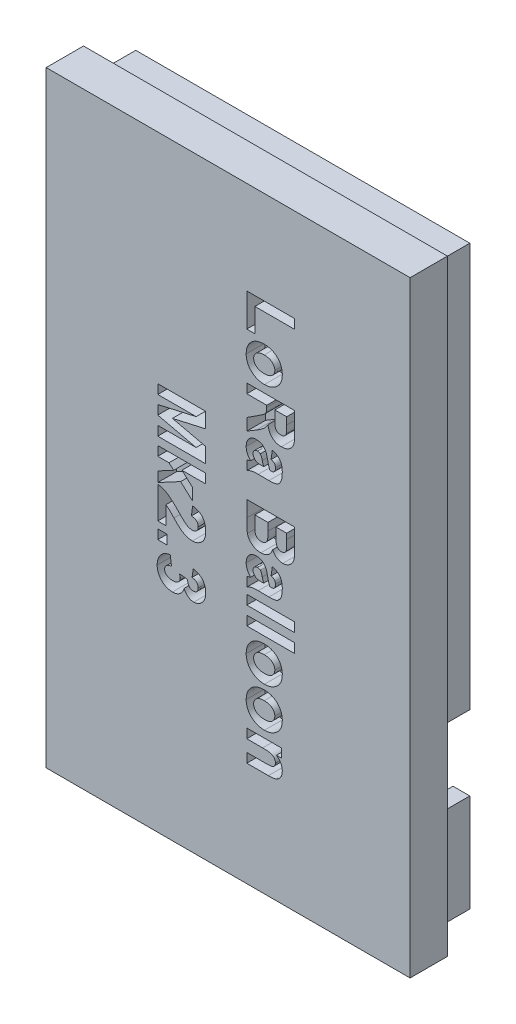
SolidWorks part; units mm, degrees
ref_plane "Front Plane" through (0, 0, 0) normal (0, 0, 1) x (1, 0, 0)
ref_plane "Top Plane" through (0, 0, 0) normal (0, 1, 0) x (1, 0, 0)
ref_plane "Right Plane" through (0, 0, 0) normal (1, 0, 0) x (0, 0, -1)
sketch "Sketch1" plane through (0, 0, 0) normal (0, 0, 1) x (1, 0, 0)
  line L1 (0, 0) -> (39, 0)
  line L2 (0, 0) -> (0, 65)
  line L3 (0, 65) -> (39, 65)
  line L4 (39, 0) -> (39, 65)
  dimension "D1" = 65
  dimension "D2" = 39
extrude "Base" add sketch "Sketch1" along normal blind 4
sketch "Sketch2" plane through (0, 0, 0) normal (0, 0, -1) x (-1, 0, 0)
  line L0 (-39, 0) -> (-39, 65) construction
  line L1 (-37.4, 63.4) -> (-35.6, 63.4)
  line L2 (-37.4, 63.4) -> (-37.4, 1.6)
  line L3 (-37.4, 1.6) -> (-35.6, 1.6)
  line L4 (-35.6, 63.4) -> (-35.6, 1.6)
  line L5 (0, 0) -> (-39, 0) construction
  line L6 (0, 65) -> (0, 0) construction
  line L7 (-35.6, 1.6) -> (-1.6, 1.6)
  line L8 (-35.6, 1.6) -> (-35.6, 3.4)
  line L9 (-35.6, 3.4) -> (-1.6, 3.4)
  line L10 (-1.6, 1.6) -> (-1.6, 3.4)
  line L12 (-39, 65) -> (0, 65) construction
  line L13 (-39, 32.5) -> (0, 32.5) construction
  line L14 (-19.5, 65) -> (-19.5, 0) construction
  line L15 (-35.6, 61.6) -> (-1.6, 61.6)
  line L16 (-1.6, 63.4) -> (-1.6, 61.6)
  line L17 (-35.6, 63.4) -> (-1.6, 63.4)
  line L18 (-35.6, 63.4) -> (-35.6, 61.6)
  line L19 (-1.6, 1.6) -> (-3.4, 1.6)
  line L20 (-3.4, 63.4) -> (-3.4, 1.6)
  line L21 (-1.6, 63.4) -> (-3.4, 63.4)
  line L22 (-1.6, 63.4) -> (-1.6, 1.6)
  dimension "D1" = 1.6
  dimension "D2" = 1.8
  dimension "D3" = 1.6
  dimension "D4" = 1.8
extrude "Mount" add sketch "Sketch2" along normal blind 4 contours L4 L1 L2 L3 | L22 L15 L20 L9 | L20 L9 L4 L7 | L9 L20 L7 L10 | L17 L20 L15 L16 | L20 L17 L4 L15
sketch "Sketch3" plane through (0, 0, 4) normal (0, 0, 1) x (1, 0, 0)
  line L0 (21.5, 0) -> (21.5, 65) construction
  line L1 (19.5, 0) -> (19.5, 5) construction
  line L2 (19.5, 65) -> (19.5, 60) construction
  line L3 (39, 65) -> (0, 65) construction
  line L4 (0, 0) -> (39, 0) construction
  line L5 (39, 32.5) -> (28, 32.5) construction
  line L6 (0, 65) -> (0, 0) construction
  line L7 (39, 0) -> (39, 65) construction
  line L8 (0, 32.5) -> (11, 32.5) construction
  text T0 "<b>  LoRa Balloon </b>\r\n<b>Mk2.3</b>" font "Arial Narrow" height in points 20
  dimension "D1" = 21.5
  dimension "D2" = 65
  dimension "D3" = 5
  dimension "D4" = 5
  dimension "D5" = 11
extrude "Name" cut sketch "Sketch3" against normal blind 2
sketch "Sketch4" plane through (35.6, 0, 0) normal (-1, 0, 0) x (0, 0, 1)
  line L0 (0, 61.6) -> (0, 3.4) construction
  line L1 (0, 20.1) -> (-4, 20.1)
  line L2 (0, 20.1) -> (0, 12.1)
  line L3 (0, 12.1) -> (-4, 12.1)
  line L4 (-4, 20.1) -> (-4, 12.1)
  line L5 (-4, 61.6) -> (-4, 3.4) construction
  line L6 (-4, 3.4) -> (0, 3.4) construction
  dimension "D1" = 16.7
  dimension "D2" = 8.7
extrude "GPS connector hole" cut sketch "Sketch4" against normal blind 1.8
sketch "Sketch5" plane through (0, 1.6, 0) normal (0, -1, 0) x (-1, 0, 0)
  line L0 (-37.4, 4) -> (-1.6, 4) construction
  line L1 (-9.1, 4) -> (-19.1, 4)
  line L2 (-9.1, 4) -> (-9.1, 0)
  line L3 (-9.1, 0) -> (-19.1, 0)
  line L4 (-19.1, 4) -> (-19.1, 0)
  line L5 (-37.4, 0) -> (-1.6, 0) construction
  line L6 (-1.6, 4) -> (-1.6, 0) construction
  dimension "D1" = 7.5
  dimension "D2" = 17.5
extrude "PWR connector hole" cut sketch "Sketch5" against normal blind 1.8
